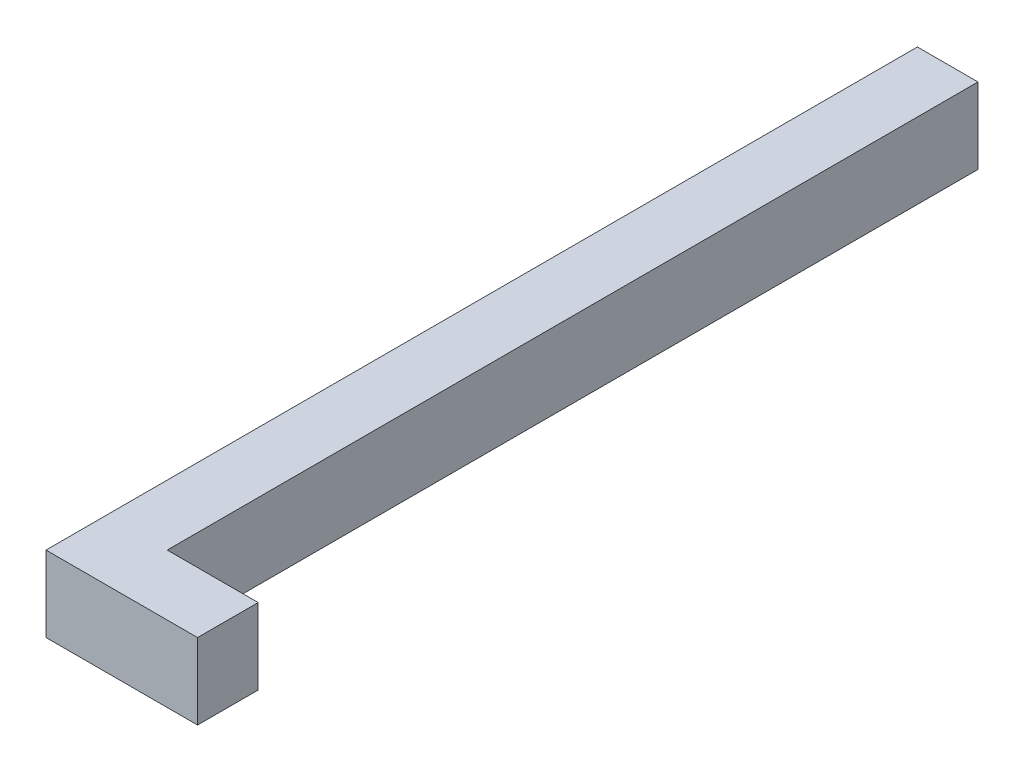
SolidWorks part; units mm, degrees
ref_plane "Front Plane" through (0, 0, 0) normal (0, 0, 1) x (1, 0, 0)
ref_plane "Top Plane" through (0, 0, 0) normal (0, 1, 0) x (1, 0, 0)
ref_plane "Right Plane" through (0, 0, 0) normal (1, 0, 0) x (0, 0, -1)
sketch "Sketch1" plane through (0, 0, 0) normal (0, 0, 1) x (1, 0, 0)
  line L1 (0, 0) -> (8, 0)
  line L2 (0, 0) -> (0, 10)
  line L3 (0, 10) -> (8, 10)
  line L4 (8, 0) -> (8, 10)
  dimension "D1" = 8
  dimension "D2" = 10
extrude "Boss-Extrude1" add sketch "Sketch1" along normal blind 115
sketch "Sketch2" plane through (0, 0, 0) normal (0, 0, -1) x (-1, 0, 0)
  line L0 (-4, 0) -> (-4, 5) construction
  line L1 (0, 0) -> (-8, 0) construction
  line L3 (-5.9, 3.1) -> (-2.1, 3.1)
  line L4 (-5.9, 3.1) -> (-5.9, 6.9)
  line L5 (-5.9, 6.9) -> (-2.1, 6.9)
  line L6 (-2.1, 3.1) -> (-2.1, 6.9)
  line L7 (-5.9, 3.1) -> (-2.1, 6.9) construction
  line L8 (-5.9, 6.9) -> (-2.1, 3.1) construction
  dimension "D1" = 5
  dimension "D2" = 3.8
  dimension "D3" = 3.8
extrude "Boss-Extrude2" add sketch "Sketch2" along normal blind 1.8
sketch "Sketch4" plane through (8, 0, 0) normal (1, 0, 0) x (0, 0, -1)
  line L0 (-115, 10) -> (0, 10) construction
  line L1 (-115, 0) -> (-107, 0)
  line L2 (-115, 0) -> (-115, 10)
  line L3 (-115, 10) -> (-107, 10)
  line L4 (-107, 0) -> (-107, 10)
  dimension "D1" = 8
extrude "Boss-Extrude4" add sketch "Sketch4" along normal blind 12
sketch "Sketch5" plane through (0, 0, 0) normal (-1, 0, 0) x (0, 0, 1)
  line L0 (0, 5) -> (30, 5) construction
  line L1 (0, 10) -> (0, 0) construction
  circle A0 centre (30, 5) radius 2.6
  dimension "D2" = 5
  dimension "D1" = 30
extrude "Cut-Extrude1" cut sketch "Sketch5" against normal blind 3
